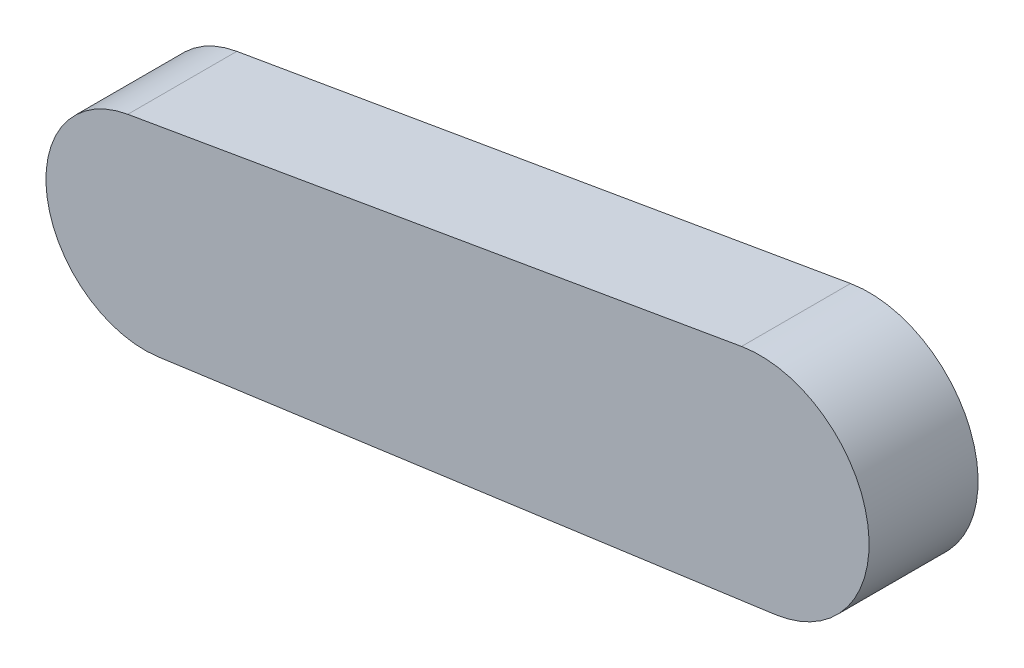
SolidWorks part; units mm, degrees
ref_plane "Front" through (0, 0, 0) normal (0, 0, 1) x (1, 0, 0)
ref_plane "Top" through (0, 0, 0) normal (0, 1, 0) x (1, 0, 0)
ref_plane "Right" through (0, 0, 0) normal (1, 0, 0) x (0, 0, -1)
sketch "Sketch1" plane through (0, 0, 0) normal (0, 0, 1) x (1, 0, 0)
  line L0 (-690.55, 507.4) -> (-991.7389, 460.6206) construction
  line L1 (-690.55, 507.4) -> (-991.7389, 460.6206)
  line L2 (-999.9394, 508.1788) -> (-699.6137, 559.9643)
  line L3 (-683.2432, 454.5628) -> (-985.128, 412.8156)
  arc A0 (-699.6137, 559.9643) -> (-683.2432, 454.5628) centre (-690.55, 507.4) cw
  arc A1 (-967.3094, 364.3132) -> (-966.8701, 364.4257) centre (-991.7389, 460.6206) ccw
  arc A2 (-999.9394, 508.1788) -> (-985.128, 412.8156) centre (-991.7389, 460.6206) ccw
  dimension "D1" = 53.34
  dimension "D2" = 48.26
extrude "Boss-Extrude1" add sketch "Sketch1" along normal blind 53.34
equation "\"mass\"= \"human weight@FS2-FR-HA-A-0001-V1, HUMAN ANALOG.Assembly\" * \"upper arm percent@FS2-FR-HA-A-0001-V1, HUMAN ANALOG.Assembly\""
